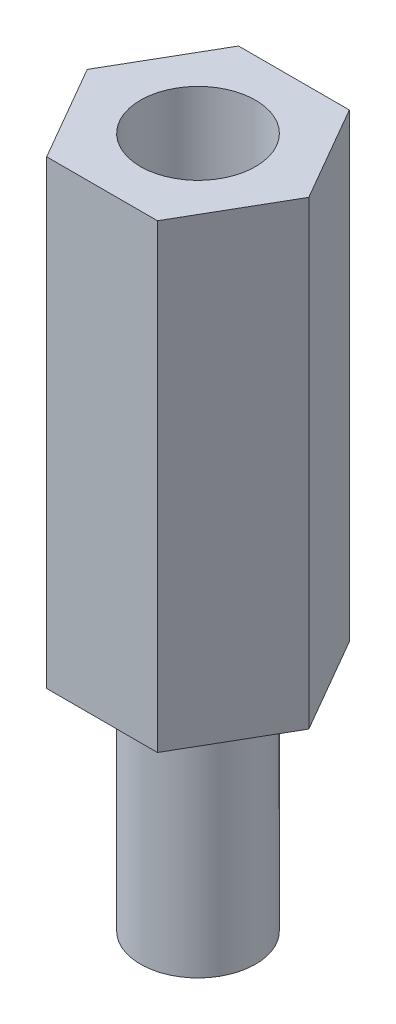
SolidWorks part; units mm, degrees
material "ABS"
ref_plane "Alzado" through (0, 0, 0) normal (0, 0, 1) x (1, 0, 0)
ref_plane "Planta" through (0, 0, 0) normal (0, 1, 0) x (1, 0, 0)
ref_plane "Vista lateral" through (0, 0, 0) normal (1, 0, 0) x (0, 0, -1)
sketch "Croquis1" plane through (0, 0, 0) normal (0, 1, 0) x (1, 0, 0)
  line L1 (1.4434, -2.5) -> (2.8868, 0)
  line L2 (2.8868, 0) -> (1.4434, 2.5)
  line L3 (1.4434, 2.5) -> (-1.4434, 2.5)
  line L4 (-1.4434, 2.5) -> (-2.8868, 0)
  line L5 (-2.8868, 0) -> (-1.4434, -2.5)
  line L6 (-1.4434, -2.5) -> (1.4434, -2.5)
  circle A0 centre (0, 0) radius 2.5 construction
  circle A1 centre (0, 0) radius 1.5
  dimension "D2" = 3
  dimension "D1" = 5
extrude "Saliente-Extruir1" add sketch "Croquis1" along normal blind 12
sketch "Croquis2" plane through (0, 0, 0) normal (0, -1, 0) x (1, 0, 0)
  circle A0 centre (0, 0) radius 1.5 construction
  circle A1 centre (0, 0) radius 1.5
extrude "Saliente-Extruir2" add sketch "Croquis2" along normal blind 6 separate body
